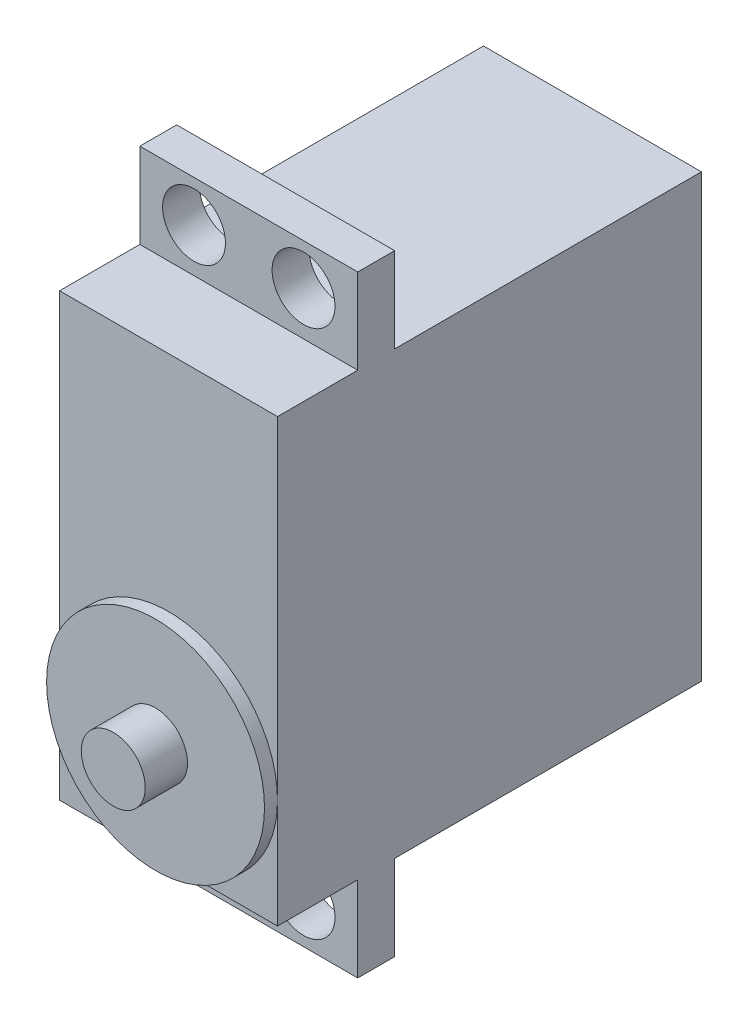
SolidWorks part; units mm, degrees
other "标注1"
sketch "草图4"
other "标注2"
sketch "草图5" plane through (-10.0501, 20.3501, -39.1001) normal (-0.0036, 0.3233, -0.9463) x (-0.9627, 0.2548, 0.0907)
ref_plane "前视基准面" through (0, 0, 0) normal (0, 0, 1) x (1, 0, 0)
ref_plane "上视基准面" through (0, 0, 0) normal (0, 1, 0) x (1, 0, 0)
ref_plane "右视基准面" through (0, 0, 0) normal (1, 0, 0) x (0, 0, -1)
other "Configuration Table"
sketch3d "3D草图2"
  line L0 (10.05, -20.35, 0) -> (10.05, -20.35, -39.1)
  line L29 (-10.05, 20.35, 0) -> (10.05, 20.35, 0)
  line L30 (-10.05, 20.35, 0) -> (-10.05, -20.35, 0)
  line L49 (-10.05, -20.35, 0) -> (10.05, -20.35, 0)
  line L50 (10.05, 20.35, 0) -> (10.05, -20.35, 0)
  line L51 (-10.05, 20.35, 0) -> (10.05, -20.35, 0) construction
  line L52 (-10.05, -20.35, 0) -> (10.05, 20.35, 0) construction
  point P0 (0, 0, 0)
  dimension "D1" = 39.1
  dimension "D2" = 20.1
  dimension "D3" = 40.7
extrude "凸台-拉伸1" add sketch "3D草图2" along direction (0, 0, -1) on the side against the normal blind 39.1 contours L30 L49 L50 L29
sketch "草图7" plane through (0, 0, 0) normal (0, 0, 1) x (1, 0, 0)
  line L0 (-10.05, -20.35) -> (0, -20.35)
  line L1 (-10.05, -20.35) -> (10.05, -20.35) construction
  line L2 (0, -20.35) -> (0, -10.3)
  circle A0 centre (0, -10.3) radius 10.05
  dimension "D2" = 10.05
extrude "凸台-拉伸2" add sketch "草图7" along normal blind 1.2
sketch "草图9" plane through (0, 0, 1.2) normal (0, 0, 1) x (1, 0, 0)
  circle A0 centre (0, -10.3) radius 2.95
  dimension "D1" = 5.9
extrude "凸台-拉伸3" add sketch "草图9" along normal blind 3.9
sketch "草图10" plane through (0, -20.35, 0) normal (0, -1, 0) x (1, 0, 0)
  line L0 (-10.05, 0) -> (-10.05, -10.8)
  line L2 (-10.05, -10.8) -> (10.05, -10.8)
  line L4 (10.05, -10.8) -> (10.05, -7.4)
  line L5 (10.05, -7.4) -> (-10.05, -7.4)
  line M7 (10.05, -39.1) -> (10.05, 0)
  dimension "D1" = 10.8
  dimension "D2" = 3.4
extrude "凸台-拉伸4" add sketch "草图10" along normal blind 7.85 contours L5 L0 L2 M7
sketch "草图11" plane through (0, 20.35, 0) normal (0, 1, 0) x (1, 0, 0)
  line L0 (-10.05, 0) -> (-10.05, 10.8)
  line L1 (-10.05, 0) -> (-10.05, 39.1) construction
  line L2 (-10.05, 10.8) -> (10.05, 10.8)
  line L3 (10.05, 0) -> (10.05, 39.1) construction
  line L4 (10.05, 10.8) -> (10.05, 7.4)
  line L5 (10.05, 7.4) -> (-10.05, 7.4)
  line M6 (-10.05, 39.1) -> (-10.05, 0)
  line M8 (10.05, 0) -> (10.05, 39.1)
  dimension "D1" = 10.8
  dimension "D2" = 3.4
extrude "凸台-拉伸5" add sketch "草图11" along normal blind 7.85 contours L5 L2 M8 M6
sketch "草图13" plane through (0, 0, -7.4) normal (0, 0, 1) x (1, 0, 0)
  line L1 (-10.05, -28.2) -> (-5.05, -28.2)
  line L2 (-10.05, -28.2) -> (-10.05, -24.4)
  line L3 (-10.05, -24.4) -> (-5.05, -24.4)
  line L4 (-5.05, -28.2) -> (-5.05, -24.4)
  line L5 (10.05, -28.2) -> (5.05, -28.2)
  line L6 (10.05, -28.2) -> (10.05, -24.4)
  line L7 (10.05, -24.4) -> (5.05, -24.4)
  line L8 (5.05, -28.2) -> (5.05, -24.4)
  circle A0 centre (-5.05, -24.4) radius 2.9
  circle A1 centre (5.05, -24.4) radius 2.9
  dimension "D5" = 5.8
  dimension "D6" = 5.8
  dimension "D1" = 5
  dimension "D2" = 5
  dimension "D3" = 3.8
  dimension "D4" = 3.8
extrude "切除-拉伸1" cut sketch "草图13" against normal up to next contours L3 A0 L4 | L4 A0 L3 | L7 A1 L8 | L8 A1 L7
sketch "草图14" plane through (0, 0, -7.4) normal (0, 0, 1) x (1, 0, 0)
  line L1 (-10.05, 28.2) -> (-5.05, 28.2)
  line L2 (-10.05, 28.2) -> (-10.05, 24.4)
  line L3 (-10.05, 24.4) -> (-5.05, 24.4)
  line L4 (-5.05, 28.2) -> (-5.05, 24.4)
  line L5 (10.05, 28.2) -> (5.05, 28.2)
  line L6 (10.05, 28.2) -> (10.05, 24.4)
  line L7 (10.05, 24.4) -> (5.05, 24.4)
  line L8 (5.05, 28.2) -> (5.05, 24.4)
  circle A0 centre (-5.05, 24.4) radius 2.9
  circle A1 centre (5.05, 24.4) radius 2.9
  dimension "D5" = 5.8
  dimension "D6" = 5.8
  dimension "D1" = 5
  dimension "D2" = 5
  dimension "D3" = 3.8
  dimension "D4" = 3.8
extrude "切除-拉伸2" cut sketch "草图14" against normal up to next contours L4 A0 L3 | L3 A0 L4 | L8 A1 L7 | L7 A1 L8
